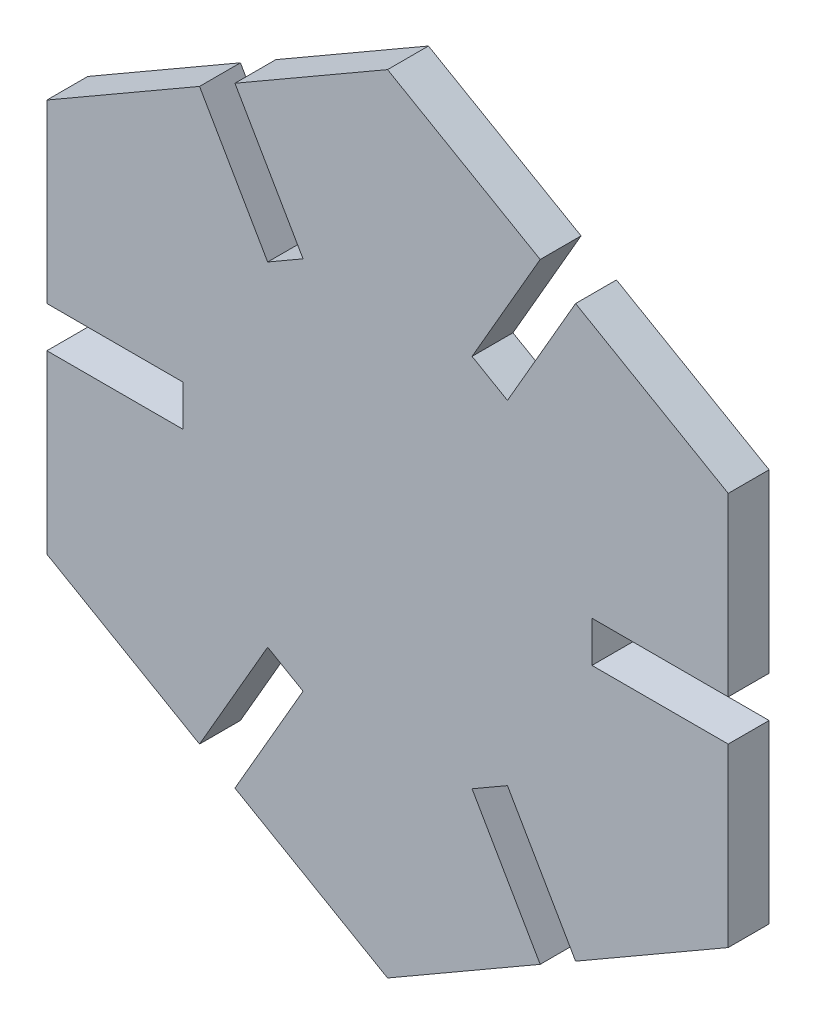
SolidWorks part; units mm, degrees
ref_plane "Front" through (0, 0, 0) normal (0, 0, 1) x (1, 0, 0)
ref_plane "Top" through (0, 0, 0) normal (0, 1, 0) x (1, 0, 0)
ref_plane "Right" through (0, 0, 0) normal (1, 0, 0) x (0, 0, -1)
sketch "Sketch1" plane through (0, 0, 0) normal (0, 0, 1) x (1, 0, 0)
  line L0 (-13.799, 20.9006) -> (-8.799, 12.2404)
  line L1 (25, 14.4338) -> (13.799, 20.9006)
  line L2 (0, 28.8675) -> (-11.201, 22.4006)
  line L3 (-25, 14.4338) -> (-25, 1.5)
  line L4 (-25, -14.4338) -> (-13.799, -20.9006)
  line L5 (0, -28.8675) -> (11.201, -22.4006)
  line L6 (25, -14.4338) -> (25, -1.5)
  line L7 (-8.799, 12.2404) -> (-6.201, 13.7404)
  line L8 (-6.201, 13.7404) -> (-11.201, 22.4006)
  line L9 (-25, 1.5) -> (-15, 1.5)
  line L10 (-15, 1.5) -> (-15, -1.5)
  line L11 (-15, -1.5) -> (-25, -1.5)
  line L12 (-13.799, -20.9006) -> (-8.799, -12.2404)
  line L13 (-8.799, -12.2404) -> (-6.201, -13.7404)
  line L14 (-6.201, -13.7404) -> (-11.201, -22.4006)
  line L15 (11.201, -22.4006) -> (6.201, -13.7404)
  line L16 (6.201, -13.7404) -> (8.799, -12.2404)
  line L17 (8.799, -12.2404) -> (13.799, -20.9006)
  line L18 (11.201, 22.4006) -> (6.201, 13.7404)
  line L19 (6.201, 13.7404) -> (8.799, 12.2404)
  line L20 (8.799, 12.2404) -> (13.799, 20.9006)
  line L21 (25, 1.5) -> (15, 1.5)
  line L22 (15, 1.5) -> (15, -1.5)
  line L23 (15, -1.5) -> (25, -1.5)
  line L24 (-13.799, 20.9006) -> (-25, 14.4338)
  line L25 (-25, -1.5) -> (-25, -14.4338)
  line L26 (-11.201, -22.4006) -> (0, -28.8675)
  line L27 (13.799, -20.9006) -> (25, -14.4338)
  line L28 (25, 1.5) -> (25, 14.4338)
  line L29 (11.201, 22.4006) -> (0, 28.8675)
  arc A0 (11.1784, 22.3616) -> (13.7765, 20.8616) centre (0, 0) ccw construction
  dimension "D2" = 50
  dimension "D3" = 10
  dimension "D4" = 3
extrude "Boss-Extrude1" add sketch "Sketch1" along normal blind 3 contours L24 L3 L9 L10 L11 L25 L4 L12 L13 L14 L26 L5 L15 L16 L17 L27 L6 L23 L22 L21 L28 L1 L20 L19 L18 L29 L2 L8 L7 L0
